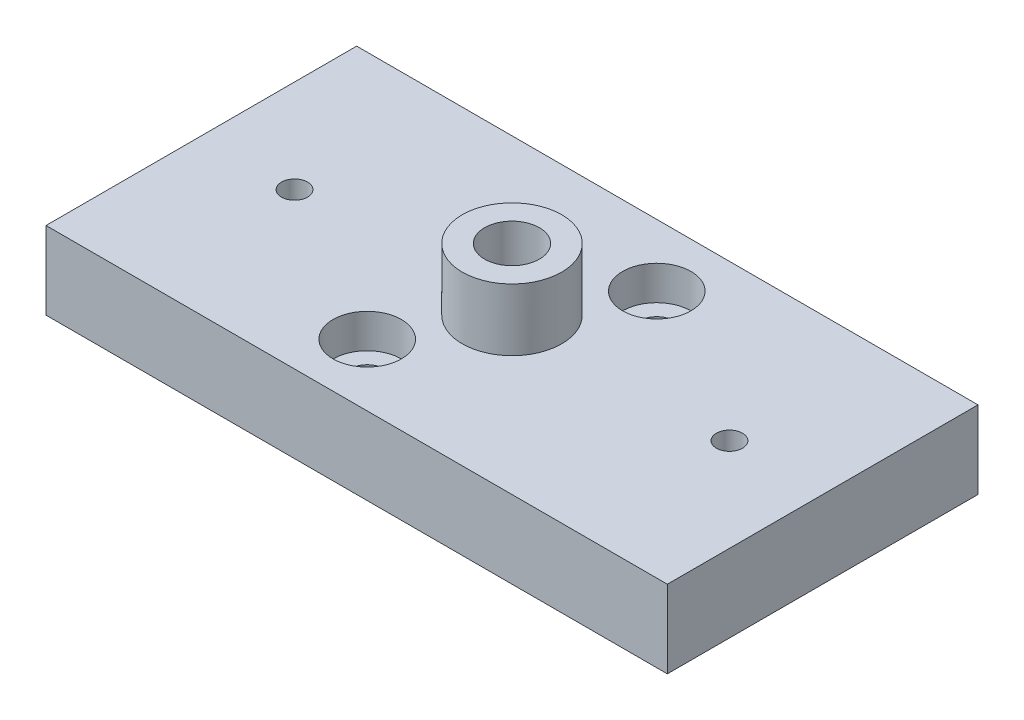
SolidWorks part; units mm, degrees
material "3003 Alloy"
ref_plane "Front Plane" through (0, 0, 0) normal (0, 0, 1) x (1, 0, 0)
ref_plane "Top Plane" through (0, 0, 0) normal (0, 1, 0) x (1, 0, 0)
ref_plane "Right Plane" through (0, 0, 0) normal (1, 0, 0) x (0, 0, -1)
sketch "Sketch1" plane through (0, 0, 0) normal (0, 1, 0) x (1, 0, 0)
  line L1 (-50, -25) -> (50, -25)
  line L2 (-50, -25) -> (-50, 25)
  line L3 (-50, 25) -> (50, 25)
  line L4 (50, -25) -> (50, 25)
  line L5 (-50, -25) -> (50, 25) construction
  line L6 (-50, 25) -> (50, -25) construction
  point P0 (0, 0)
  dimension "D1" = 100
  dimension "D2" = 50
extrude "Boss-Extrude1" add sketch "Sketch1" along normal blind 12.5
sketch "Sketch2" plane through (0, 12.5, 0) normal (0, 1, 0) x (1, 0, 0)
  circle A0 centre (0, 0) radius 8
  dimension "D1" = 16
extrude "Boss-Extrude2" add sketch "Sketch2" along normal blind 10
hole_wizard "M10x1.25 Tapped Hole1" positions "Sketch3" profile "Sketch4" tap size "M10x1.25" standard "ISO"
sketch "Sketch3" plane through (0, 22.5, 0) normal (0, 1, 0) x (1, 0, 0)
  point P0 (0, 0)
sketch "Sketch4" plane through (0, 22.5, 0) normal (1, 0, 0) x (0, 0, 1)
  line L0 (0, 0) -> (0, 15.6438)
  line L1 (0, 15.6438) -> (4.4, 13)
  line L2 (4.4, 13) -> (4.4, 0)
  line L5 (4.4, 0) -> (0, 0)
  line L10 (0, 15.6438) -> (-4.4, 13) construction
  line L11 (0, -6.35) -> (0, 107.95) construction
  dimension "Tap Drill Dia." = 8.8
  dimension "Tap Drill Depth" = 13
  dimension "Drill Angle" = 118
cosmetic thread "Hole Thread1" parameters "D1"=13, "D2"=10
sketch "Sketch5" plane through (0, 12.5, 0) normal (0, 1, 0) x (1, 0, 0)
  line L0 (-35, 0) -> (35, 0) construction
  point P3 (-35, 0)
  point P4 (0, 0)
  point P5 (35, 0)
  dimension "D1" = 70
hole_wizard "M5 Tapped Hole1" positions "Sketch6" profile "Sketch7" tap size "M5" standard "ISO"
sketch "Sketch6" plane through (0, 12.5, 0) normal (0, 1, 0) x (1, 0, 0)
  point P0 (-35, 0)
  point P3 (35, 0)
sketch "Sketch7" plane through (-35, 12.5, 0) normal (1, 0, 0) x (0, 0, 1)
  line L0 (0, 0) -> (0, 11.2618)
  line L1 (0, 11.2618) -> (2.1, 10)
  line L2 (2.1, 10) -> (2.1, 0)
  line L5 (2.1, 0) -> (0, 0)
  line L10 (0, 11.2618) -> (-2.1, 10) construction
  line L11 (0, -6.35) -> (0, 107.95) construction
  dimension "Tap Drill Dia." = 4.2
  dimension "Tap Drill Depth" = 10
  dimension "Drill Angle" = 118
cosmetic thread "Hole Thread2" parameters "D1"=10, "D2"=5
cosmetic thread "Hole Thread3" parameters "D1"=10, "D2"=5
sketch "Sketch8" plane through (0, 0, 0) normal (0, -1, 0) x (1, 0, 0)
  line L0 (8.3, -15) -> (-8.3, 15) construction
  line L1 (-50, 0) -> (50, 0) construction
  line L2 (-50, -25) -> (-50, 25) construction
  line L3 (50, 25) -> (50, -25) construction
  circle A0 centre (8.3, -15) radius 2.75
  circle A1 centre (-8.3, 15) radius 2.75
  point P7 (0, 0)
  dimension "D1" = 5.5
  dimension "D2" = 34.2864
  dimension "D3" = 118.957
extrude "Cut-Extrude1" cut sketch "Sketch8" against normal through all
sketch "Sketch10" plane through (0, 12.5, 0) normal (0, 1, 0) x (1, 0, 0)
  circle A0 centre (8.3, 15) radius 5.5
  circle A1 centre (-8.3, -15) radius 5.5
  dimension "D1" = 11
extrude "Cut-Extrude2" cut sketch "Sketch10" against normal blind 5.5
